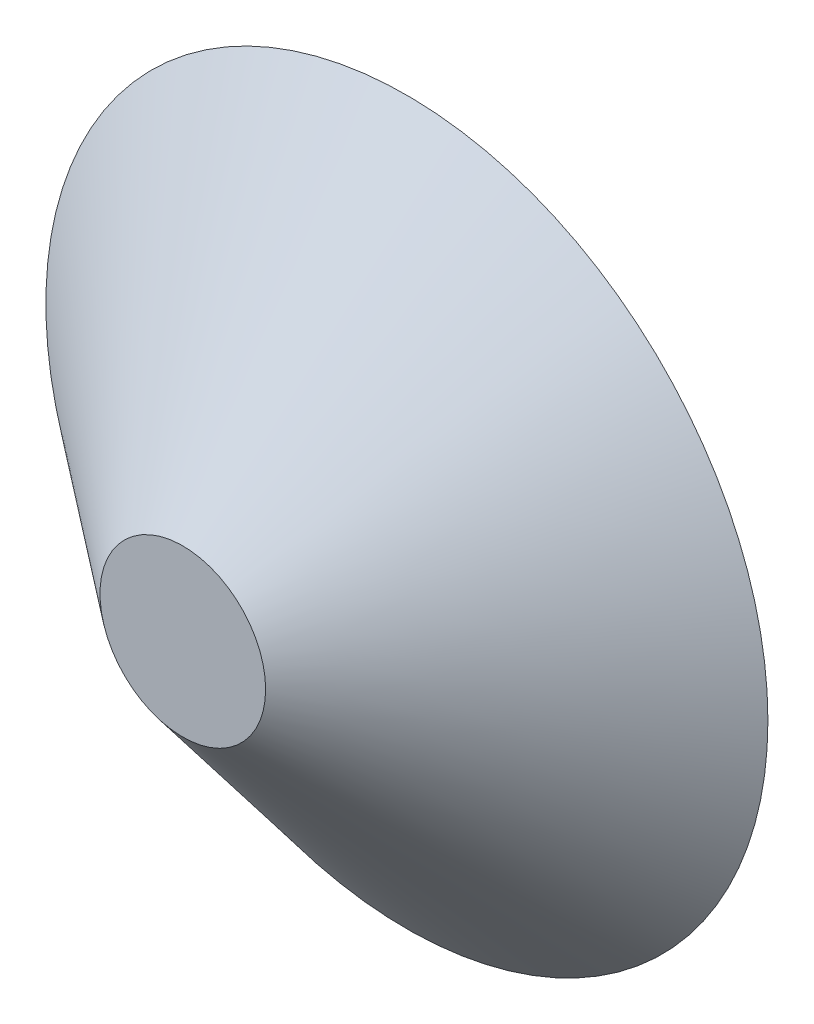
SolidWorks part; units mm, degrees
material "Tantalum"
ref_plane "Front" through (0, 0, 0) normal (0, 0, 1) x (1, 0, 0)
ref_plane "Top" through (0, 0, 0) normal (0, 1, 0) x (1, 0, 0)
ref_plane "Right" through (0, 0, 0) normal (1, 0, 0) x (0, 0, -1)
sketch "Sketch1" plane through (0, 0, 0) normal (0, 0, 1) x (1, 0, 0)
  circle A0 centre (0, 0) radius 82.9698
extrude "Boss-Extrude4" add sketch "Sketch1" along normal blind 51.5 draft 51.15
